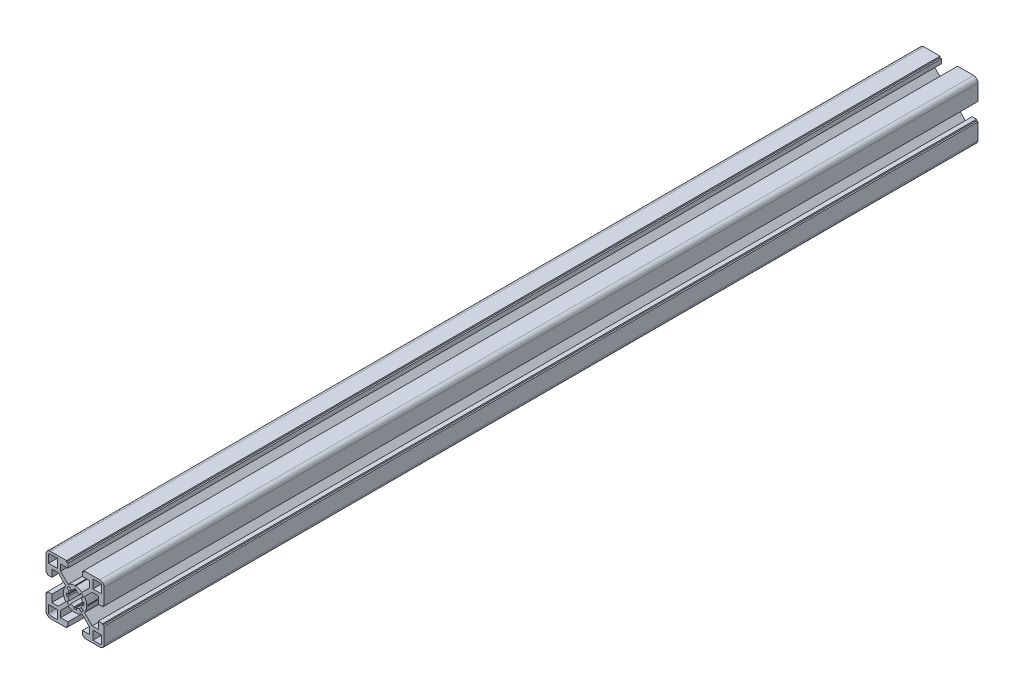
SolidWorks part; units mm, degrees
ref_plane "Plan de face" through (0, 0, 0) normal (0, 0, 1) x (1, 0, 0)
ref_plane "Plan de dessus" through (0, 0, 0) normal (0, 1, 0) x (1, 0, 0)
ref_plane "Plan de droite" through (0, 0, 0) normal (1, 0, 0) x (0, 0, -1)
ref_plane "Plan1" through (0, 0, 100) normal (0, 0, 1) x (1, 0, 0)
sketch "Esquisse1" plane through (0, 0, 100) normal (0, 0, 1) x (1, 0, 0)
  line L0 (18.25, 12.25) -> (12.25, 12.25)
  line L1 (12.25, 12.25) -> (12.25, 18.25)
  line L2 (12.25, 18.25) -> (17.25, 18.25)
  line L3 (18.25, 17.25) -> (18.25, 12.25)
  line L4 (-18.25, -12.25) -> (-12.25, -12.25)
  line L5 (-12.25, -12.25) -> (-12.25, -18.25)
  line L6 (-12.25, -18.25) -> (-17.25, -18.25)
  line L7 (-18.25, -17.25) -> (-18.25, -12.25)
  line L8 (6, -19) -> (6, -20)
  line L9 (6, -20) -> (17, -20)
  line L10 (20, -17) -> (20, -6)
  line L11 (20, -6) -> (19, -6)
  line L12 (19, -6) -> (19, -5)
  line L13 (19, -5) -> (16, -5)
  line L14 (16, -5) -> (16, -10)
  line L15 (16, -10) -> (11.6971, -10)
  line L16 (11.6971, -10) -> (6.4414, -4.7443)
  line L17 (7.9941, -0.3064) -> (7.7, 0)
  line L18 (7.7, 0) -> (7.9941, 0.3064)
  line L19 (6.4414, 4.7443) -> (11.6971, 10)
  line L20 (11.6971, 10) -> (16, 10)
  line L21 (16, 10) -> (16, 5)
  line L22 (16, 5) -> (19, 5)
  line L23 (19, 5) -> (19, 6)
  line L24 (19, 6) -> (20, 6)
  line L25 (20, 6) -> (20, 17)
  line L26 (17, 20) -> (6, 20)
  line L27 (6, 20) -> (6, 19)
  line L28 (6, 19) -> (5, 19)
  line L29 (5, 19) -> (5, 16)
  line L30 (5, 16) -> (10, 16)
  line L31 (10, 16) -> (10, 11.6971)
  line L32 (10, 11.6971) -> (4.7443, 6.4414)
  line L33 (0.3064, 7.9941) -> (0, 7.7)
  line L34 (0, 7.7) -> (-0.3064, 7.9941)
  line L35 (-4.7443, 6.4414) -> (-10, 11.6971)
  line L36 (-10, 11.6971) -> (-10, 16)
  line L37 (-10, 16) -> (-5, 16)
  line L38 (-5, 16) -> (-5, 19)
  line L39 (-5, 19) -> (-6, 19)
  line L40 (-6, 19) -> (-6, 20)
  line L41 (-6, 20) -> (-17, 20)
  line L42 (-20, 17) -> (-20, 6)
  line L43 (-20, 6) -> (-19, 6)
  line L44 (-19, 6) -> (-19, 5)
  line L45 (-19, 5) -> (-16, 5)
  line L46 (-16, 5) -> (-16, 10)
  line L47 (-16, 10) -> (-11.6971, 10)
  line L48 (-11.6971, 10) -> (-6.4414, 4.7443)
  line L49 (-7.9941, 0.3064) -> (-7.7, 0)
  line L50 (-7.7, 0) -> (-7.9941, -0.3064)
  line L51 (-6.4414, -4.7443) -> (-11.6971, -10)
  line L52 (-11.6971, -10) -> (-16, -10)
  line L53 (-16, -10) -> (-16, -5)
  line L54 (-16, -5) -> (-19, -5)
  line L55 (-19, -5) -> (-19, -6)
  line L56 (-19, -6) -> (-20, -6)
  line L57 (-20, -6) -> (-20, -17)
  line L58 (-17, -20) -> (-6, -20)
  line L59 (-6, -20) -> (-6, -19)
  line L60 (-6, -19) -> (-5, -19)
  line L61 (-5, -19) -> (-5, -16)
  line L62 (-5, -16) -> (-10, -16)
  line L63 (-10, -16) -> (-10, -11.6971)
  line L64 (-10, -11.6971) -> (-4.7443, -6.4414)
  line L65 (-0.3064, -7.9941) -> (0, -7.7)
  line L66 (0, -7.7) -> (0.3064, -7.9941)
  line L67 (4.7443, -6.4414) -> (10, -11.6971)
  line L68 (10, -11.6971) -> (10, -16)
  line L69 (10, -16) -> (5, -16)
  line L70 (5, -16) -> (5, -19)
  line L71 (5, -19) -> (6, -19)
  line L72 (-12.25, 18.25) -> (-12.25, 12.25)
  line L73 (-12.25, 12.25) -> (-18.25, 12.25)
  line L74 (-18.25, 12.25) -> (-18.25, 17.25)
  line L75 (-17.25, 18.25) -> (-12.25, 18.25)
  line L76 (12.25, -18.25) -> (12.25, -12.25)
  line L77 (12.25, -12.25) -> (18.25, -12.25)
  line L78 (18.25, -12.25) -> (18.25, -17.25)
  line L79 (17.25, -18.25) -> (12.25, -18.25)
  line L80 (-5.7057, -4.0552) -> (-4.0755, -2.8966)
  line L81 (-4.9435, -0.7494) -> (-5.9322, -0.8993)
  line L82 (-5.9322, 0.8993) -> (-4.9435, 0.7494)
  line L83 (-4.0755, 2.8966) -> (-5.7057, 4.0552)
  line L84 (-4.0641, 5.6994) -> (-2.903, 4.071)
  line L85 (-0.7494, 4.9435) -> (-0.8993, 5.9322)
  line L86 (0.8993, 5.9322) -> (0.7494, 4.9435)
  line L87 (2.903, 4.071) -> (4.0641, 5.6994)
  line L88 (5.7057, 4.0552) -> (4.0755, 2.8966)
  line L89 (4.9435, 0.7494) -> (5.9322, 0.8993)
  line L90 (5.9322, -0.8993) -> (4.9435, -0.7494)
  line L91 (4.0755, -2.8966) -> (5.7057, -4.0552)
  line L92 (4.0641, -5.6994) -> (2.903, -4.071)
  line L93 (0.7494, -4.9435) -> (0.8993, -5.9322)
  line L94 (-0.8993, -5.9322) -> (-0.7494, -4.9435)
  line L95 (-2.903, -4.071) -> (-4.0641, -5.6994)
  arc A0 (17.25, 18.25) -> (18.25, 17.25) centre (17.25, 17.25) cw
  arc A1 (-17.25, -18.25) -> (-18.25, -17.25) centre (-17.25, -17.25) cw
  arc A2 (17, -20) -> (20, -17) centre (17, -17) ccw
  arc A3 (6.4414, -4.7443) -> (7.9941, -0.3064) centre (0, 0) ccw
  arc A4 (7.9941, 0.3064) -> (6.4414, 4.7443) centre (0, 0) ccw
  arc A5 (20, 17) -> (17, 20) centre (17, 17) ccw
  arc A6 (4.7443, 6.4414) -> (0.3064, 7.9941) centre (0, 0) ccw
  arc A7 (-0.3064, 7.9941) -> (-4.7443, 6.4414) centre (0, 0) ccw
  arc A8 (-17, 20) -> (-20, 17) centre (-17, 17) ccw
  arc A9 (-6.4414, 4.7443) -> (-7.9941, 0.3064) centre (0, 0) ccw
  arc A10 (-7.9941, -0.3064) -> (-6.4414, -4.7443) centre (0, 0) ccw
  arc A11 (-20, -17) -> (-17, -20) centre (-17, -17) ccw
  arc A12 (-4.7443, -6.4414) -> (-0.3064, -7.9941) centre (0, 0) ccw
  arc A13 (0.3064, -7.9941) -> (4.7443, -6.4414) centre (0, 0) ccw
  arc A14 (-18.25, 17.25) -> (-17.25, 18.25) centre (-17.25, 17.25) cw
  arc A15 (18.25, -17.25) -> (17.25, -18.25) centre (17.25, -17.25) cw
  arc A16 (-4.0641, -5.6994) -> (-5.7057, -4.0552) centre (0, 0) cw
  arc A17 (-4.0755, -2.8966) -> (-4.9435, -0.7494) centre (0, 0) cw
  arc A18 (-5.9322, -0.8993) -> (-5.9322, 0.8993) centre (0, 0) cw
  arc A19 (-4.9435, 0.7494) -> (-4.0755, 2.8966) centre (0, 0) cw
  arc A20 (-5.7057, 4.0552) -> (-4.0641, 5.6994) centre (0, 0) cw
  arc A21 (-2.903, 4.071) -> (-0.7494, 4.9435) centre (0, 0) cw
  arc A22 (-0.8993, 5.9322) -> (0.8993, 5.9322) centre (0, 0) cw
  arc A23 (0.7494, 4.9435) -> (2.903, 4.071) centre (0, 0) cw
  arc A24 (4.0641, 5.6994) -> (5.7057, 4.0552) centre (0, 0) cw
  arc A25 (4.0755, 2.8966) -> (4.9435, 0.7494) centre (0, 0) cw
  arc A26 (5.9322, 0.8993) -> (5.9322, -0.8993) centre (0, 0) cw
  arc A27 (4.9435, -0.7494) -> (4.0755, -2.8966) centre (0, 0) cw
  arc A28 (5.7057, -4.0552) -> (4.0641, -5.6994) centre (0, 0) cw
  arc A29 (2.903, -4.071) -> (0.7494, -4.9435) centre (0, 0) cw
  arc A30 (0.8993, -5.9322) -> (-0.8993, -5.9322) centre (0, 0) cw
  arc A31 (-0.7494, -4.9435) -> (-2.903, -4.071) centre (0, 0) cw
extrude "Boss.-Extru.1" add sketch "Esquisse1" against normal blind 600
